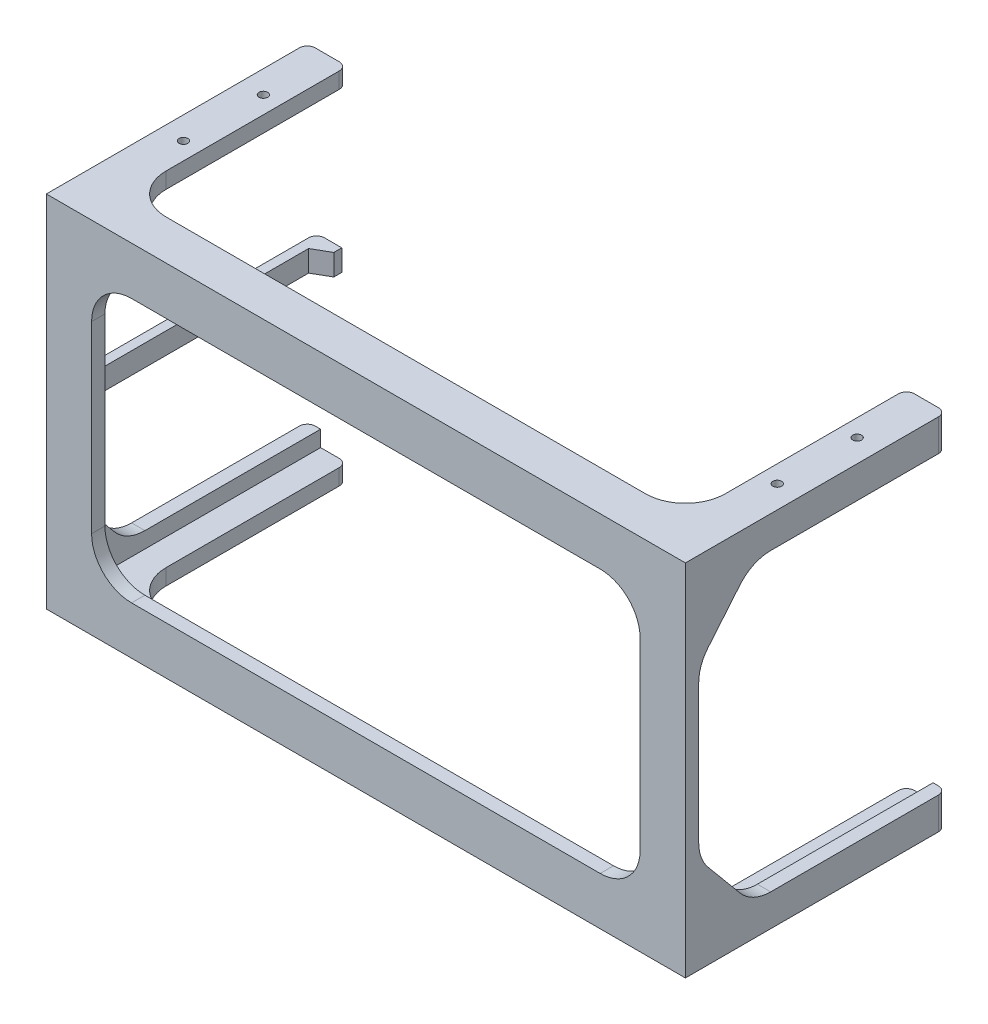
SolidWorks part; units mm, degrees
material "PLA Polyacetic Acid"
ref_plane "Front Plane" through (0, 0, 0) normal (0, 0, 1) x (1, 0, 0)
ref_plane "Top Plane" through (0, 0, 0) normal (0, 1, 0) x (1, 0, 0)
ref_plane "Right Plane" through (0, 0, 0) normal (1, 0, 0) x (0, 0, -1)
sketch "Sketch1" plane through (0, 0, 0) normal (0, 0, 1) x (1, 0, 0)
  line L0 (-103, -49.5) -> (-103, 49.5)
  line L1 (-115, -61.5) -> (115, -61.5)
  line L2 (-115, -61.5) -> (-115, 61.5)
  line L3 (-115, 61.5) -> (115, 61.5)
  line L4 (115, -61.5) -> (115, 61.5)
  line L5 (-115, -61.5) -> (115, 61.5) construction
  line L6 (-115, 61.5) -> (115, -61.5) construction
  line L7 (-103, 49.5) -> (103, 49.5)
  line L8 (103, -49.5) -> (103, 49.5)
  line L9 (-103, -49.5) -> (103, -49.5)
  point P0 (0, 0)
  dimension "D1" = 123
  dimension "D2" = 230
  dimension "D3" = 12
extrude "Boss-Extrude1" add sketch "Sketch1" along normal blind 5
sketch "Sketch2" plane through (0, 61.5, 0) normal (0, 1, 0) x (1, 0, 0)
  line L0 (0, -5) -> (0, 39.233) construction
  line L1 (-115, -5) -> (115, -5)
  line L2 (-115, -5) -> (-115, 10)
  line L3 (-105, 10) -> (105, 10)
  line L4 (115, -5) -> (115, 10)
  line L5 (-115, 10) -> (-105, 10) construction
  line L6 (-115, 10) -> (-115, 93)
  line L7 (-115, 93) -> (-105, 93)
  line L8 (-105, 10) -> (-105, 93)
  line L9 (115, -5) -> (-115, -5) construction
  line L10 (105, 10) -> (105, 93)
  line L11 (115, 93) -> (105, 93)
  line L12 (115, 10) -> (115, 93)
  line L13 (115, 10) -> (105, 10) construction
  line L14 (115, -5) -> (115, 10)
  line L15 (-115, 10) -> (-105, 10) construction
  line L16 (105, 10) -> (115, 10) construction
  line L17 (115, 0) -> (-115, 0) construction
  point P1 (-115, -4)
  point P18 (113.8653, 8.1789)
  line M7 (115, 0) -> (-115, 0)
  line M8 (-115, 0) -> (-115, -5)
  line M9 (-115, -5) -> (115, -5)
  line M10 (115, -5) -> (115, 0)
  dimension "D1" = 10
  dimension "D2" = 10
  dimension "D3" = 93
extrude "Boss-Extrude2" add sketch "Sketch2" along normal blind 6 contours L4 L12 L11 L10 L3 L8 L7 L6 L2 M7 | M10 M7 M8 M9
mirror "Mirror1" about plane through (0, 0, 0) normal (0, 1, 0) of "Boss-Extrude2"
sketch "Sketch3" plane through (-115, 0, 0) normal (-1, 0, 0) x (0, 0, 1)
  line L0 (-25, 61.5) -> (0, 31.5)
  line L1 (0, 61.5) -> (-25, 61.5) construction
  line L2 (0, 61.5) -> (0, 31.5) construction
  line L5 (0, 0) -> (-30.8852, 0) construction
  line L6 (0, -61.5) -> (0, -31.5)
  line L7 (0, -61.5) -> (-25, -61.5)
  line L8 (-25, -61.5) -> (0, -31.5)
  line L9 (-93, 61.5) -> (-93, 55.5)
  line L10 (-93, 55.5) -> (-20, 55.5)
  line L11 (-93, -55.5) -> (-20, -55.5)
  line L12 (-93, -61.5) -> (-93, -55.5)
  line L17 (0, 61.5) -> (0, -61.5)
  line L18 (0, -61.5) -> (-93, -61.5)
  line L19 (-93, -61.5) -> (-93, -67.5)
  line L20 (-93, -67.5) -> (5, -67.5)
  line L21 (5, -67.5) -> (5, 67.5)
  line L22 (5, 67.5) -> (-93, 67.5)
  line L23 (-93, 67.5) -> (-93, 61.5)
  line L24 (-93, 61.5) -> (0, 61.5)
  line L25 (0, 61.5) -> (0, -61.5)
  line L26 (0, -61.5) -> (-93, -61.5)
  line L27 (-93, -61.5) -> (-93, -67.5)
  line L28 (-93, -67.5) -> (5, -67.5)
  line L29 (5, -67.5) -> (5, 67.5)
  line L30 (5, 67.5) -> (-93, 67.5)
  line L31 (-93, 67.5) -> (-93, 61.5)
  line L32 (-93, 61.5) -> (0, 61.5)
  line M1 (0, 61.5) -> (0, -61.5)
  line M2 (0, -61.5) -> (-93, -61.5)
  line M3 (-93, -61.5) -> (-93, -67.5)
  line M4 (-93, -67.5) -> (5, -67.5)
  line M5 (5, -67.5) -> (5, 67.5)
  line M6 (5, 67.5) -> (-93, 67.5)
  line M7 (-93, 67.5) -> (-93, 61.5)
  line M8 (-93, 61.5) -> (0, 61.5)
  dimension "D1" = 30
  dimension "D2" = 25
  dimension "D3" = 0
  dimension "D4" = 6
extrude "Boss-Extrude3" add sketch "Sketch3" along normal blind 5 contours M8 M1 M2 M3 M4 M5 M6 M7 | L0 M8 M1 | L8 M2 M1 | L9 L10 L0 M8 | L12 L8 L11 M2
mirror "Mirror2" about plane through (0, 0, 0) normal (1, 0, 0) of "Boss-Extrude3"
fillet "Fillet1" radius 15 16 edges at (117.5, 55.5, -20) (117.5, -55.5, -20) (117.5, -31.5, 0) (117.5, 31.5, 0) (-103, -49.5, 2.5) (103, -49.5, 2.5) (103, 49.5, 2.5) (-103, 49.5, 2.5) (105, 64.5, -10) (-105, 64.5, -10) (-105, -64.5, -10) (105, -64.5, -10) (-117.5, 55.5, -20) (-117.5, 31.5, 0) (-117.5, -31.5, 0) (-117.5, -55.5, -20)
sketch "Sketch4" plane through (0, 0, 0) normal (0, 1, 0) x (1, 0, 0)
  line L0 (115, 0) -> (120, 0) construction
  line L1 (-120, 96.4641) -> (-116.5, 96.4641)
  line L2 (-120, 96.4641) -> (-120, 0)
  line L3 (-120, 0) -> (-116.5, 0)
  line L4 (-116.5, 96.4641) -> (-116.5, 0)
  line L6 (-116.5, 90) -> (-110.5, 93.4641)
  line L7 (-110.5, 93.4641) -> (-110.5, 96.4641)
  line L8 (-110.5, 96.4641) -> (-116.5, 96.4641)
  line L11 (0, 0) -> (0, 73.181) construction
  point P6 (0, 0)
  point P7 (0, 0)
  dimension "D1" = 3.5
  dimension "D2" = 3
  dimension "D3" = 60
  dimension "D4" = 90
  dimension "D5" = 221
extrude "Boss-Extrude4" add sketch "Sketch4" along normal mid plane 8 contours L7 L8 L4 L6
fillet "Fillet2" radius 5 2 edges at (-118.25, -4, 0) (-118.25, 4, 0)
fillet "Fillet3" radius 3 9 edges at (120, 61.5, -93) (120, -61.5, -93) (105, 64.5, -93) (-120, 0, -96.4641) (-105, 64.5, -93) (-105, -64.5, -93) (105, -64.5, -93) (-120, -61.5, -93) (-120, 61.5, -93)
hole_wizard "CSK for #4 Flat Head Machine Screw1" positions "Sketch5" profile "Sketch6" countersink size "#4" standard "ANSI Inch" end condition up to next
sketch "Sketch5" plane through (0, 61.5, 0) normal (0, -1, 0) x (1, 0, 0)
  line L0 (111.5, -68) -> (111.5, -38) construction
  line L3 (111.5, -68) -> (111.5, -93) construction
  line L4 (115, -93) -> (108, -93) construction
  line L6 (0, 0) -> (0, -52.6747) construction
  line L8 (115, 0) -> (-115, 0) construction
  point P0 (111.5, -68)
  point P2 (111.5, -38)
  point P21 (-111.5, -38)
  point P22 (-111.5, -68)
  point P24 (0, 0)
  dimension "D1" = 30
  dimension "D2" = 25
sketch "Sketch6" plane through (111.5, 61.5, -68) normal (1, 0, 0) x (0, 0, -1)
  line L0 (0, 0) -> (0, 6)
  line L1 (0, 6) -> (1.6319, 6)
  line L2 (1.6319, 6) -> (1.6319, 2.4098)
  line L3 (1.6319, 2.4098) -> (2.8575, 1)
  line L4 (2.8575, 1) -> (2.8575, 0)
  line L6 (2.8575, 0) -> (0, 0)
  line L7 (-1.632, 2.4098) -> (-2.8575, 1) construction
  line L11 (0, -6.35) -> (0, 107.95) construction
  dimension "Thru Hole Dia." = 3.2639
  dimension "Thru Hole Depth" = 6
  dimension "C'Sink Dia." = 5.715
  dimension "C'Sink Angle" = 82
  dimension "Head Clearance" = 1
